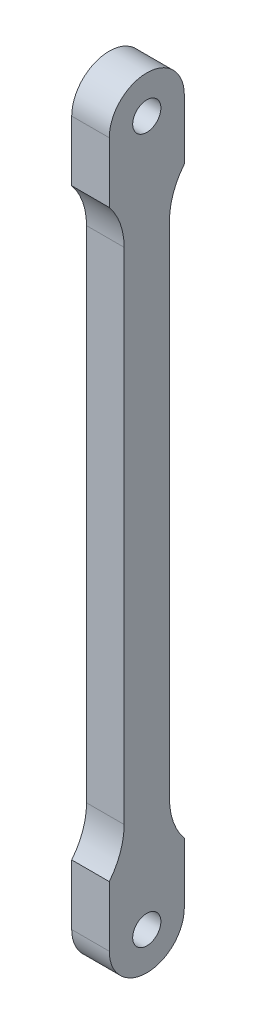
SolidWorks part; units mm, degrees
ref_plane "前视基准面" through (0, 0, 0) normal (0, 0, 1) x (1, 0, 0)
ref_plane "上视基准面" through (0, 0, 0) normal (0, 1, 0) x (1, 0, 0)
ref_plane "右视基准面" through (0, 0, 0) normal (1, 0, 0) x (0, 0, -1)
sketch "Sketch1" plane through (0, 0, 0) normal (1, 0, 0) x (0, 0, -1)
  circle A0 centre (2.9834, 10.8268) radius 7.75 construction
  circle A1 centre (2.9834, 10.8268) radius 6.25 construction
  circle A2 centre (2.9834, 18.5768) radius 0.8
  circle A3 centre (2.9834, 3.0768) radius 0.8
  circle A4 centre (-3.2666, 10.8268) radius 0.8
  circle A5 centre (9.2334, 10.8268) radius 0.8
  circle A6 centre (2.9834, 10.8268) radius 10
  circle A7 centre (2.9834, 10.8268) radius 3.3018
  dimension "D1" = 15.5
  dimension "D2" = 12.5
  dimension "D3" = 20
extrude "Boss-Extrude1" add sketch "Sketch1" along normal blind 1.5
sketch "Sketch2" plane through (0, 0, 0) normal (-1, 0, 0) x (0, 0, 1)
  line L0 (-2.9834, 10.8268) -> (-2.9834, 25.4318) construction
  line L2 (-12.9834, 95.8916) -> (7.0166, 95.8916) construction
  line L3 (-12.9834, 95.8916) -> (-12.9834, 10.8268) construction
  line L4 (-12.9834, 10.8268) -> (7.0166, 10.8268) construction
  line L5 (7.0166, 95.8916) -> (7.0166, 10.8268) construction
  line L6 (-12.9834, 95.8916) -> (7.0166, 10.8268) construction
  line L7 (-12.9834, 10.8268) -> (7.0166, 95.8916) construction
  line L8 (-15.5319, 95.8916) -> (9.5652, 95.8916)
  line L9 (-15.5319, 95.8916) -> (-15.5319, 10.8268)
  line L10 (-15.5319, 10.8268) -> (9.5652, 10.8268) construction
  line L11 (9.5652, 95.8916) -> (9.5652, 10.8268)
  line L12 (-15.5319, 95.8916) -> (9.5652, 10.8268) construction
  line L13 (-15.5319, 10.8268) -> (9.5652, 95.8916) construction
  circle A0 centre (-2.9834, 10.8268) radius 10 construction
  arc A1 (-12.9834, 10.8268) -> (7.0166, 10.8268) centre (-2.9834, 10.8268) cw construction
  circle A2 centre (-2.9834, 10.8268) radius 12.5485 construction
  circle A3 centre (-2.9834, 10.8268) radius 10
  arc A4 (-15.5319, 10.8268) -> (9.5652, 10.8268) centre (-2.9834, 10.8268) ccw
  circle A5 centre (-2.9834, 10.8268) radius 0.6321 construction
  point P1 (-2.9834, 53.3592)
  point P12 (-2.9834, 53.3592)
  dimension "D1" = 0
extrude "Boss-Extrude2" add sketch "Sketch2" against normal blind 9
sketch "Sketch3" plane through (9, 0, 0) normal (1, 0, 0) x (0, 0, -1)
  line L0 (2.9834, 95.8916) -> (2.9834, 22.8694) construction
  line L3 (-3.0511, 36.1504) -> (-3.0511, 97.5726)
  line L4 (-3.0511, 97.5726) -> (-16.389, 97.5726)
  line L5 (-16.389, 97.5726) -> (-16.389, 8.1411)
  line L6 (-16.389, 8.1411) -> (-9.5652, 10.8268)
  line L7 (22.3558, 8.1411) -> (15.5319, 10.8268)
  line L8 (22.3558, 97.5726) -> (22.3558, 8.1411)
  line L9 (9.0179, 97.5726) -> (22.3558, 97.5726)
  line L10 (9.0179, 36.1504) -> (9.0179, 97.5726)
  circle A0 centre (2.9834, 90.4737) radius 1.5
  spline S0 degree 3 poles (-9.5652, 10.8268) (-9.6442, 15.1222) (-6.9162, 23.507) (-3.4283, 31.5617) (-3.0511, 36.1504) knots 0 0 0 0 0.482385 1 1 1 1
  spline S1 degree 3 poles (15.5319, 10.8268) (15.611, 15.1222) (12.883, 23.507) (9.395, 31.5617) (9.0179, 36.1504) knots 0 0 0 0 0.482385 1 1 1 1
extrude "Cut-Extrude1" cut sketch "Sketch3" against normal through all both and the other way through all
fillet "Fillet1" radius 5 2 edges at (4.5, 95.8916, -9.0179) (4.5, 95.8916, 3.0511)
sketch "Sketch4" plane through (9, 0, 0) normal (1, 0, 0) x (0, 0, -1)
  line L0 (2.9834, 85.8493) -> (31.7006, 85.8493) construction
  line L1 (2.9834, 10.8493) -> (27.5415, 10.8493) construction
  line L2 (34.7795, 85.8493) -> (34.7795, 10.8493) construction
  line L3 (38.7736, 85.8493) -> (38.7736, 10.8493)
  line L4 (30.7854, 85.8493) -> (30.7854, 10.8493)
  circle A0 centre (34.7795, 85.8493) radius 1.5
  circle A1 centre (34.7795, 10.8493) radius 1.5
  arc A2 (38.7736, 85.8493) -> (30.7854, 85.8493) centre (34.7795, 85.8493) ccw
  arc A3 (30.7854, 10.8493) -> (38.7736, 10.8493) centre (34.7795, 10.8493) ccw
  point P10 (34.7795, 48.3493)
  dimension "D1" = 75
extrude "Boss-Extrude3" add sketch "Sketch4" along normal blind 4 separate body
sketch "Sketch5" plane through (9, 0, 0) normal (1, 0, 0) x (0, 0, -1)
  line L1 (-23.8752, 97.3072) -> (19.9117, 97.3072)
  line L2 (-23.8752, 97.3072) -> (-23.8752, -8.1795)
  line L3 (-23.8752, -8.1795) -> (19.9117, -8.1795)
  line L4 (19.9117, 97.3072) -> (19.9117, -8.1795)
extrude "Cut-Extrude2" cut sketch "Sketch5" against normal through all both and the other way through all
sketch "Sketch6" plane through (13, 0, 0) normal (1, 0, 0) x (0, 0, -1)
  line L0 (34.7795, 89.8434) -> (34.7795, 94.1424) construction
  line L1 (30.7854, 85.8493) -> (30.7854, 10.8493) construction
  line L2 (43.2356, 74.9571) -> (18.3353, 74.9571) construction
  line L3 (43.2356, 74.9571) -> (43.2356, 21.7415) construction
  line L4 (43.2356, 21.7415) -> (18.3353, 21.7415) construction
  line L5 (18.3353, 74.9571) -> (18.3353, 21.7415) construction
  line L6 (43.2356, 74.9571) -> (18.3353, 21.7415) construction
  line L7 (43.2356, 21.7415) -> (18.3353, 74.9571) construction
  line L8 (25.2691, 74.9571) -> (25.2691, 21.7415) construction
  line L9 (32.3688, 74.9571) -> (32.3688, 21.7415)
  line L10 (18.1695, 74.9571) -> (18.1695, 21.7415)
  line L11 (44.2899, 74.9571) -> (44.2899, 21.7415) construction
  line L12 (37.1903, 74.9571) -> (37.1903, 21.7415)
  line L13 (51.3896, 74.9571) -> (51.3896, 21.7415)
  arc A0 (37.1903, 74.9571) -> (51.3896, 74.9571) centre (44.2899, 74.9571) cw
  arc A1 (32.3688, 74.9571) -> (18.1695, 74.9571) centre (25.2691, 74.9571) ccw
  arc A2 (18.1695, 21.7415) -> (32.3688, 21.7415) centre (25.2691, 21.7415) ccw
  arc A3 (51.3896, 21.7415) -> (37.1903, 21.7415) centre (44.2899, 21.7415) cw
  point P1 (30.7854, 48.3493)
  point P12 (25.2691, 48.3493)
  point P21 (44.2899, 48.3493)
extrude "Cut-Extrude3" cut sketch "Sketch6" against normal through all both and the other way through all
